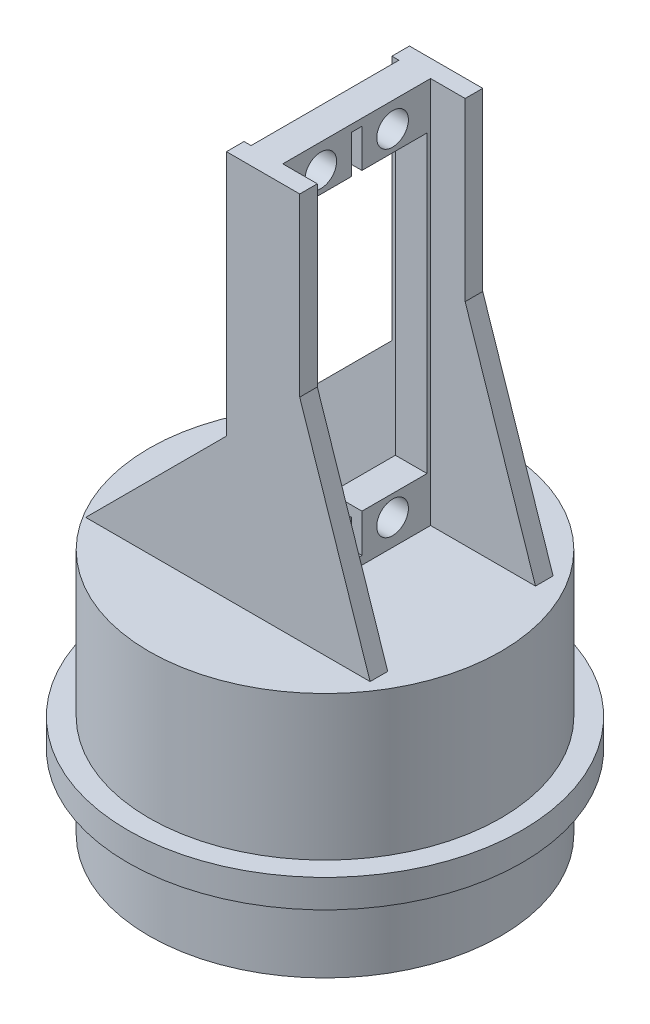
SolidWorks part; units mm, degrees
ref_plane "Front Plane" through (0, 0, 0) normal (0, 0, 1) x (1, 0, 0)
ref_plane "Top Plane" through (0, 0, 0) normal (0, 1, 0) x (1, 0, 0)
ref_plane "Right Plane" through (0, 0, 0) normal (1, 0, 0) x (0, 0, -1)
sketch "Sketch1" plane through (0, 0, 0) normal (0, 0, 1) x (1, 0, 0)
  line L0 (25, 14.5) -> (28, 14.5)
  line L1 (0, 35) -> (25, 35)
  line L2 (0, 0) -> (25, 0)
  line L3 (25, 35) -> (25, 0)
  line L4 (28, 14.5) -> (28, 10.5)
  line L5 (28, 10.5) -> (25, 10.5)
  line L6 (0, 35) -> (0, 0)
  dimension "D1" = 35
  dimension "D2" = 3
  dimension "D3" = 4
  dimension "D4" = 25
  dimension "D5" = 10.5
revolve "Revolve1" add sketch "Sketch1" angle 360 about L6
sketch "Sketch2" plane through (0, 35, 0) normal (0, 1, 0) x (1, 0, 0)
  line L0 (4.5, 13) -> (4.5, -13)
  line L1 (9.4096, -13) -> (0, -13)
  line L2 (9.4096, -13) -> (9.4096, 13)
  line L3 (9.4096, 13) -> (0, 13)
  line L4 (0, -13) -> (0, 13)
  line L5 (9.4096, -13) -> (0, 13) construction
  line L6 (9.4096, 13) -> (0, -13) construction
  line L7 (9.4096, 10.5) -> (4.5, 10.5)
  line L8 (4.5, -10.5) -> (9.4096, -10.5)
  line L9 (0, 13) -> (-1, 13)
  line L10 (-1, 13) -> (-1, 10.5)
  line L11 (-1, 10.5) -> (0, 10.5)
  line L12 (0, -13) -> (-1, -13)
  line L13 (-1, -13) -> (-1, -10.5)
  line L14 (-1, -10.5) -> (0, -10.5)
  point P0 (4.7048, 0)
  dimension "D1" = 9.4096
  dimension "D2" = 4.5
  dimension "D3" = 26
  dimension "D4" = 2.5
  dimension "D5" = 2.5
  dimension "D6" = 1
extrude "Boss-Extrude1" add sketch "Sketch2" along normal blind 55 contours L4 L1 L0 L3 | L7 L2 L3 L0 | L8 L0 L1 L2 | L14 L13 L12 L4 | L10 L11 L4 L9
chamfer "Chamfer1" distance 10 distance2 30 2 edges at (9.4096, 35, 11.75) (9.4096, 35, -11.75)
chamfer "Chamfer2" distance 20 angle 45 2 edges at (-1, 35, -11.75) (-1, 35, 11.75)
sketch "Sketch3" plane through (4.5, 0, 0) normal (1, 0, 0) x (0, 0, -1)
  line L0 (-5.1, 86.5) -> (-5.1, 38.7) construction
  line L1 (-10, 89) -> (10, 89)
  line L2 (-10, 89) -> (-10, 36.2)
  line L3 (-10, 36.2) -> (10, 36.2)
  line L4 (10, 89) -> (10, 36.2)
  line L5 (-10, 89) -> (10, 36.2) construction
  line L6 (-10, 36.2) -> (10, 89) construction
  line L7 (10.5, 90) -> (-10.5, 90) construction
  line L8 (10, 41.643) -> (-10, 41.643)
  line L9 (10, 41.643) -> (10, 83.557)
  line L10 (10, 83.557) -> (-10, 83.557)
  line L11 (-10, 41.643) -> (-10, 83.557)
  line L12 (10, 41.643) -> (-10, 83.557) construction
  line L13 (10, 83.557) -> (-10, 41.643) construction
  line L14 (-0.75, 83.557) -> (0.75, 83.557)
  line L15 (-0.75, 83.557) -> (-0.75, 89)
  line L16 (-0.75, 89) -> (0.75, 89)
  line L17 (0.75, 83.557) -> (0.75, 89)
  line L18 (-0.751, 41.643) -> (0.75, 41.643)
  line L19 (-0.751, 41.643) -> (-0.751, 36.2)
  line L20 (-0.751, 36.2) -> (0.75, 36.2)
  line L21 (0.75, 41.643) -> (0.75, 36.2)
  circle A0 centre (-5.1, 86.5) radius 2.25
  circle A1 centre (5.1, 86.5) radius 2.25
  circle A2 centre (-5.1, 38.7) radius 2.25
  circle A3 centre (5.1, 38.7) radius 2.25
  point P0 (0, 62.6)
  point P11 (0, 72.6)
  point P14 (-5.1, 62.6)
  point P15 (0, 62.6)
  point P28 (0, 89)
  point P29 (0, 62.9276)
  point P32 (0, 90)
  dimension "D3" = 4.5
  dimension "D1" = 52.8
  dimension "D2" = 20
  dimension "D4" = 10.2
  dimension "D5" = 4.9
  dimension "D6" = 13.9
  dimension "D7" = 33.9
  dimension "D8" = 0.75
  dimension "D9" = 0.75
  dimension "D10" = 1
extrude "Cut-Extrude1" cut sketch "Sketch3" against normal blind 55 contours L4 L10 L2 L8 | A0 | A1 | A3 | A2 | L21 L8 L19 L3 | L10 L17 L1 L15
sketch "Sketch5" plane through (0, 35, 0) normal (0, 1, 0) x (1, 0, 0)
  line L0 (-21, -10.5) -> (0, -10.5) construction
  line L1 (0, 10.5) -> (-15.6827, 10.5)
  line L2 (0, 10.5) -> (0, -10.5)
  line L3 (0, -10.5) -> (-15.6827, -10.5)
  line L4 (-15.6827, 10.5) -> (-15.6827, -10.5)
extrude "Cut-Extrude2" cut sketch "Sketch5" against normal through all
